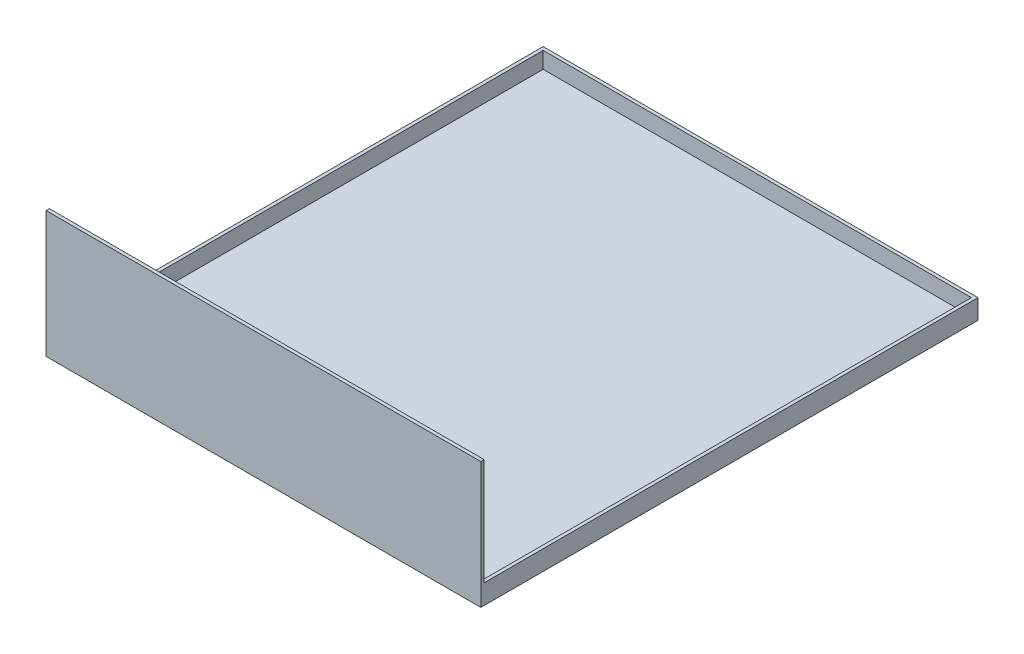
SolidWorks part; units mm, degrees
ref_plane "Front Plane" through (0, 0, 0) normal (0, 0, 1) x (1, 0, 0)
ref_plane "Top Plane" through (0, 0, 0) normal (0, 1, 0) x (1, 0, 0)
ref_plane "Right Plane" through (0, 0, 0) normal (1, 0, 0) x (0, 0, -1)
sketch "Sketch1" plane through (0, 0, 0) normal (0, 0, 1) x (1, 0, 0)
  line L1 (-132.5, 31) -> (132.5, 31)
  line L2 (-132.5, 31) -> (-132.5, -31)
  line L3 (-132.5, -31) -> (132.5, -31)
  line L4 (132.5, 31) -> (132.5, -31)
  line L5 (-132.5, 31) -> (132.5, -31) construction
  line L6 (-132.5, -31) -> (132.5, 31) construction
  point P0 (0, 0)
  dimension "D1" = 62
  dimension "D2" = 265
extrude "Boss-Extrude1" add sketch "Sketch1" along normal blind 303
shell "Shell1" thickness 2
sketch "Sketch2" plane through (0, 31, 0) normal (0, 1, 0) x (1, 0, 0)
  line L0 (132.5, -303) -> (132.5, 0) construction
  line L1 (-132.5, 0) -> (132.5, 0)
  line L2 (-132.5, 0) -> (-132.5, -301)
  line L3 (-132.5, -301) -> (132.5, -301)
  line L4 (132.5, 0) -> (132.5, -301)
extrude "Cut-Extrude1" cut sketch "Sketch2" against normal blind 50
sketch "Sketch3" plane through (0, 31, 0) normal (0, 1, 0) x (1, 0, 0)
  line L1 (-132.5, -301) -> (132.5, -301)
  line L2 (-132.5, -301) -> (-132.5, -303)
  line L3 (-132.5, -303) -> (132.5, -303)
  line L4 (132.5, -301) -> (132.5, -303)
extrude "Boss-Extrude2" add sketch "Sketch3" along normal blind 15
